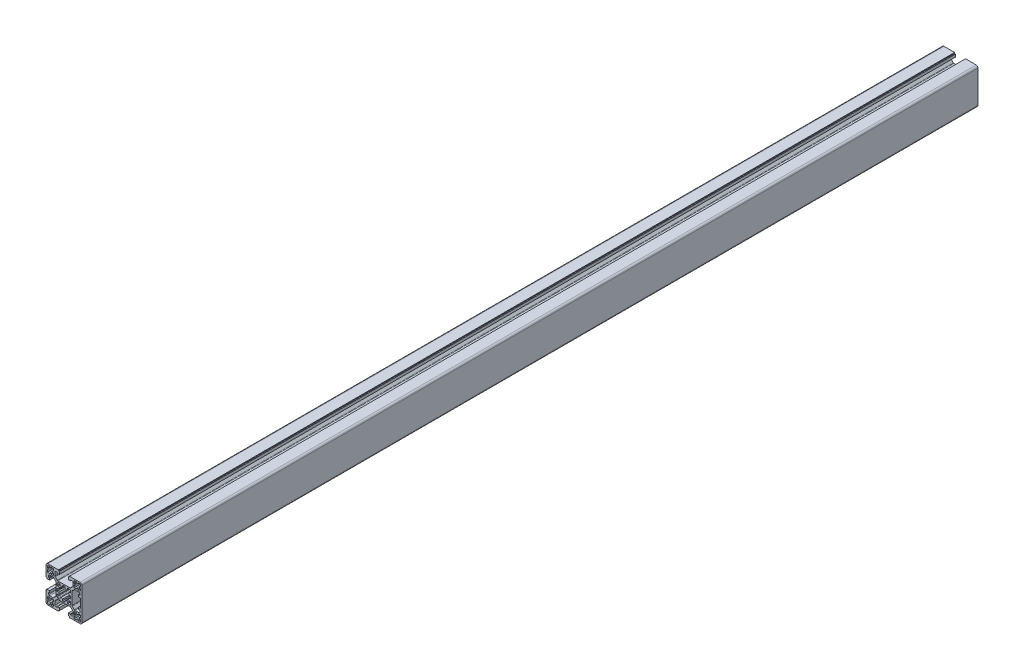
SolidWorks part; units mm, degrees
ref_plane "前视基准面" through (0, 0, 0) normal (0, 0, 1) x (1, 0, 0)
ref_plane "上视基准面" through (0, 0, 0) normal (0, 1, 0) x (1, 0, 0)
ref_plane "右视基准面" through (0, 0, 0) normal (1, 0, 0) x (0, 0, -1)
sketch "草图1" plane through (0, 0, 0) normal (0, 0, 1) x (1, 0, 0)
  line L0 (1011.2421, 717.8553) -> (1012.8421, 717.8553)
  line L1 (1015.5421, 689.5553) -> (1014.5421, 689.5553)
  line L2 (1015.5421, 686.8553) -> (1015.5421, 689.5553)
  line L3 (1012.8421, 686.8553) -> (1015.5421, 686.8553)
  line L4 (1012.8421, 687.8553) -> (1012.8421, 686.8553)
  line L5 (1011.2421, 687.8553) -> (1012.8421, 687.8553)
  line L6 (1011.2421, 686.8553) -> (1011.2421, 687.8553)
  line L7 (1009.5421, 686.8553) -> (1011.2421, 686.8553)
  line L8 (1008.5421, 689.5553) -> (1008.5421, 687.8553)
  line L9 (1009.5421, 689.5553) -> (1008.5421, 689.5553)
  line L10 (1009.5421, 691.1553) -> (1009.5421, 689.5553)
  line L11 (1008.5421, 691.1553) -> (1009.5421, 691.1553)
  line L12 (1008.5421, 693.8553) -> (1008.5421, 691.1553)
  line L13 (1011.2421, 693.8553) -> (1008.5421, 693.8553)
  line L14 (1011.2421, 692.8553) -> (1011.2421, 693.8553)
  line L15 (1012.8421, 692.8553) -> (1011.2421, 692.8553)
  line L16 (1012.8421, 693.8553) -> (1012.8421, 692.8553)
  line L17 (1015.5421, 693.8553) -> (1012.8421, 693.8553)
  line L18 (1015.5421, 691.1553) -> (1015.5421, 693.8553)
  line L19 (1014.5421, 691.1553) -> (1015.5421, 691.1553)
  line L20 (1014.5421, 689.5553) -> (1014.5421, 691.1553)
  line L21 (1042.8421, 693.8553) -> (1042.8421, 692.8553)
  line L22 (1045.5421, 693.8553) -> (1042.8421, 693.8553)
  line L23 (1045.5421, 691.1553) -> (1045.5421, 693.8553)
  line L24 (1044.5421, 691.1553) -> (1045.5421, 691.1553)
  line L25 (1044.5421, 689.5553) -> (1044.5421, 691.1553)
  line L26 (1045.5421, 689.5553) -> (1044.5421, 689.5553)
  line L27 (1045.5421, 687.8553) -> (1045.5421, 689.5553)
  line L28 (1042.8421, 686.8553) -> (1044.5421, 686.8553)
  line L29 (1042.8421, 687.8553) -> (1042.8421, 686.8553)
  line L30 (1041.2421, 687.8553) -> (1042.8421, 687.8553)
  line L31 (1041.2421, 686.8553) -> (1041.2421, 687.8553)
  line L32 (1038.5421, 686.8553) -> (1041.2421, 686.8553)
  line L33 (1038.5421, 689.5553) -> (1038.5421, 686.8553)
  line L34 (1039.5421, 689.5553) -> (1038.5421, 689.5553)
  line L35 (1039.5421, 691.1553) -> (1039.5421, 689.5553)
  line L36 (1038.5421, 691.1553) -> (1039.5421, 691.1553)
  line L37 (1038.5421, 693.8553) -> (1038.5421, 691.1553)
  line L38 (1041.2421, 693.8553) -> (1038.5421, 693.8553)
  line L39 (1041.2421, 692.8553) -> (1041.2421, 693.8553)
  line L40 (1042.8421, 692.8553) -> (1041.2421, 692.8553)
  line L41 (1025.6421, 697.8553) -> (1028.4421, 697.8553)
  line L42 (1025.6421, 699.5209) -> (1025.6421, 697.8553)
  line L43 (1022.8421, 699.1754) -> (1023.9066, 700.2398)
  line L44 (1022.8421, 697.8553) -> (1022.8421, 699.1754)
  line L45 (1020.5421, 697.8553) -> (1022.8421, 697.8553)
  line L46 (1019.5421, 701.1553) -> (1019.5421, 698.8553)
  line L47 (1020.8622, 701.1553) -> (1019.5421, 701.1553)
  line L48 (1021.9267, 702.2197) -> (1020.8622, 701.1553)
  line L49 (1019.5421, 703.9553) -> (1021.2078, 703.9553)
  line L50 (1019.5421, 706.7553) -> (1019.5421, 703.9553)
  line L51 (1021.2078, 706.7553) -> (1019.5421, 706.7553)
  line L52 (1020.8622, 709.5553) -> (1021.9267, 708.4909)
  line L53 (1019.5421, 709.5553) -> (1020.8622, 709.5553)
  line L54 (1019.5421, 711.8553) -> (1019.5421, 709.5553)
  line L55 (1022.8421, 712.8553) -> (1020.5421, 712.8553)
  line L56 (1022.8421, 711.5352) -> (1022.8421, 712.8553)
  line L57 (1023.9066, 710.4708) -> (1022.8421, 711.5352)
  line L58 (1025.6421, 712.8553) -> (1025.6421, 711.1897)
  line L59 (1028.4421, 712.8553) -> (1025.6421, 712.8553)
  line L60 (1028.4421, 711.1897) -> (1028.4421, 712.8553)
  line L61 (1031.2421, 711.5352) -> (1030.1777, 710.4708)
  line L62 (1031.2421, 712.8553) -> (1031.2421, 711.5352)
  line L63 (1033.5421, 712.8553) -> (1031.2421, 712.8553)
  line L64 (1034.5421, 709.5553) -> (1034.5421, 711.8553)
  line L65 (1033.222, 709.5553) -> (1034.5421, 709.5553)
  line L66 (1032.1576, 708.4909) -> (1033.222, 709.5553)
  line L67 (1034.5421, 706.7553) -> (1032.8765, 706.7553)
  line L68 (1034.5421, 703.9553) -> (1034.5421, 706.7553)
  line L69 (1032.8765, 703.9553) -> (1034.5421, 703.9553)
  line L70 (1033.222, 701.1553) -> (1032.1576, 702.2197)
  line L71 (1034.5421, 701.1553) -> (1033.222, 701.1553)
  line L72 (1034.5421, 698.8553) -> (1034.5421, 701.1553)
  line L73 (1031.2421, 697.8553) -> (1033.5421, 697.8553)
  line L74 (1031.2421, 699.1754) -> (1031.2421, 697.8553)
  line L75 (1030.1777, 700.2398) -> (1031.2421, 699.1754)
  line L76 (1028.4421, 697.8553) -> (1028.4421, 699.5209)
  line L77 (1043.0421, 700.2553) -> (1045.5421, 700.2553)
  line L78 (1043.0421, 698.2553) -> (1043.0421, 700.2553)
  line L79 (1045.0421, 698.2553) -> (1043.0421, 698.2553)
  line L80 (1045.0421, 696.3553) -> (1045.0421, 698.2553)
  line L81 (1039.2241, 695.3553) -> (1044.0421, 695.3553)
  line L82 (1036.335, 697.8302) -> (1038.517, 695.6482)
  line L83 (1036.0421, 712.1733) -> (1036.0421, 698.5373)
  line L84 (1038.517, 715.0624) -> (1036.335, 712.8804)
  line L85 (1044.0421, 715.3553) -> (1039.2241, 715.3553)
  line L86 (1045.0421, 712.4553) -> (1045.0421, 714.3553)
  line L87 (1043.0421, 712.4553) -> (1045.0421, 712.4553)
  line L88 (1043.0421, 710.4553) -> (1043.0421, 712.4553)
  line L89 (1045.5421, 710.4553) -> (1043.0421, 710.4553)
  line L90 (1045.5421, 700.2553) -> (1045.5421, 710.4553)
  line L91 (1019.9421, 688.3553) -> (1019.9421, 689.3553)
  line L92 (1018.0421, 688.3553) -> (1019.9421, 688.3553)
  line L93 (1017.0421, 693.1733) -> (1017.0421, 689.3553)
  line L94 (1019.517, 696.0624) -> (1017.335, 693.8804)
  line L95 (1033.8602, 696.3553) -> (1020.2241, 696.3553)
  line L96 (1036.7492, 693.8804) -> (1034.5673, 696.0624)
  line L97 (1037.0421, 689.3553) -> (1037.0421, 693.1733)
  line L98 (1034.1421, 688.3553) -> (1036.0421, 688.3553)
  line L99 (1034.1421, 689.3553) -> (1034.1421, 688.3553)
  line L100 (1032.1421, 689.3553) -> (1034.1421, 689.3553)
  line L101 (1032.1421, 686.3553) -> (1032.1421, 689.3553)
  line L102 (1033.1421, 686.3553) -> (1032.1421, 686.3553)
  line L103 (1033.1421, 685.3553) -> (1033.1421, 686.3553)
  line L104 (1045.0421, 685.3553) -> (1033.1421, 685.3553)
  line L105 (1047.0421, 723.3553) -> (1047.0421, 687.3553)
  line L106 (1033.1421, 725.3553) -> (1045.0421, 725.3553)
  line L107 (1033.1421, 724.3553) -> (1033.1421, 725.3553)
  line L108 (1032.1421, 724.3553) -> (1033.1421, 724.3553)
  line L109 (1032.1421, 721.3553) -> (1032.1421, 724.3553)
  line L110 (1034.1421, 721.3553) -> (1032.1421, 721.3553)
  line L111 (1034.1421, 722.3553) -> (1034.1421, 721.3553)
  line L112 (1036.0421, 722.3553) -> (1034.1421, 722.3553)
  line L113 (1037.0421, 717.5373) -> (1037.0421, 721.3553)
  line L114 (1034.5673, 714.6482) -> (1036.7492, 716.8302)
  line L115 (1020.2241, 714.3553) -> (1033.8602, 714.3553)
  line L116 (1017.335, 716.8302) -> (1019.517, 714.6482)
  line L117 (1017.0421, 721.3553) -> (1017.0421, 717.5373)
  line L118 (1019.9421, 722.3553) -> (1018.0421, 722.3553)
  line L119 (1019.9421, 721.3553) -> (1019.9421, 722.3553)
  line L120 (1021.9421, 721.3553) -> (1019.9421, 721.3553)
  line L121 (1021.9421, 724.3553) -> (1021.9421, 721.3553)
  line L122 (1020.9421, 724.3553) -> (1021.9421, 724.3553)
  line L123 (1020.9421, 725.3553) -> (1020.9421, 724.3553)
  line L124 (1009.0421, 725.3553) -> (1020.9421, 725.3553)
  line L125 (1007.0421, 711.4553) -> (1007.0421, 723.3553)
  line L126 (1008.0421, 711.4553) -> (1007.0421, 711.4553)
  line L127 (1008.0421, 710.4553) -> (1008.0421, 711.4553)
  line L128 (1011.0421, 710.4553) -> (1008.0421, 710.4553)
  line L129 (1011.0421, 712.4553) -> (1011.0421, 710.4553)
  line L130 (1010.0421, 712.4553) -> (1011.0421, 712.4553)
  line L131 (1010.0421, 714.3553) -> (1010.0421, 712.4553)
  line L132 (1014.8602, 715.3553) -> (1011.0421, 715.3553)
  line L133 (1017.7492, 712.8804) -> (1015.5673, 715.0624)
  line L134 (1018.0421, 698.5373) -> (1018.0421, 712.1733)
  line L135 (1015.5673, 695.6482) -> (1017.7492, 697.8302)
  line L136 (1011.0421, 695.3553) -> (1014.8602, 695.3553)
  line L137 (1010.0421, 698.2553) -> (1010.0421, 696.3553)
  line L138 (1011.0421, 698.2553) -> (1010.0421, 698.2553)
  line L139 (1011.0421, 700.2553) -> (1011.0421, 698.2553)
  line L140 (1008.0421, 700.2553) -> (1011.0421, 700.2553)
  line L141 (1008.0421, 699.2553) -> (1008.0421, 700.2553)
  line L142 (1007.0421, 699.2553) -> (1008.0421, 699.2553)
  line L143 (1007.0421, 687.3553) -> (1007.0421, 699.2553)
  line L144 (1020.9421, 685.3553) -> (1009.0421, 685.3553)
  line L145 (1020.9421, 686.3553) -> (1020.9421, 685.3553)
  line L146 (1021.9421, 686.3553) -> (1020.9421, 686.3553)
  line L147 (1021.9421, 689.3553) -> (1021.9421, 686.3553)
  line L148 (1019.9421, 689.3553) -> (1021.9421, 689.3553)
  line L149 (1038.5421, 721.1553) -> (1039.5421, 721.1553)
  line L150 (1038.5421, 723.8553) -> (1038.5421, 721.1553)
  line L151 (1041.2421, 723.8553) -> (1038.5421, 723.8553)
  line L152 (1041.2421, 722.8553) -> (1041.2421, 723.8553)
  line L153 (1042.8421, 722.8553) -> (1041.2421, 722.8553)
  line L154 (1042.8421, 723.8553) -> (1042.8421, 722.8553)
  line L155 (1044.5421, 723.8553) -> (1042.8421, 723.8553)
  line L156 (1045.5421, 721.1553) -> (1045.5421, 722.8553)
  line L157 (1044.5421, 721.1553) -> (1045.5421, 721.1553)
  line L158 (1044.5421, 719.5553) -> (1044.5421, 721.1553)
  line L159 (1045.5421, 719.5553) -> (1044.5421, 719.5553)
  line L160 (1045.5421, 716.8553) -> (1045.5421, 719.5553)
  line L161 (1042.8421, 716.8553) -> (1045.5421, 716.8553)
  line L162 (1042.8421, 717.8553) -> (1042.8421, 716.8553)
  line L163 (1041.2421, 717.8553) -> (1042.8421, 717.8553)
  line L164 (1041.2421, 716.8553) -> (1041.2421, 717.8553)
  line L165 (1038.5421, 716.8553) -> (1041.2421, 716.8553)
  line L166 (1038.5421, 719.5553) -> (1038.5421, 716.8553)
  line L167 (1039.5421, 719.5553) -> (1038.5421, 719.5553)
  line L168 (1039.5421, 721.1553) -> (1039.5421, 719.5553)
  line L169 (1011.2421, 716.8553) -> (1011.2421, 717.8553)
  line L170 (1008.5421, 716.8553) -> (1011.2421, 716.8553)
  line L171 (1008.5421, 719.5553) -> (1008.5421, 716.8553)
  line L172 (1009.5421, 719.5553) -> (1008.5421, 719.5553)
  line L173 (1009.5421, 721.1553) -> (1009.5421, 719.5553)
  line L174 (1008.5421, 721.1553) -> (1009.5421, 721.1553)
  line L175 (1008.5421, 722.8553) -> (1008.5421, 721.1553)
  line L176 (1011.2421, 723.8553) -> (1009.5421, 723.8553)
  line L177 (1011.2421, 722.8553) -> (1011.2421, 723.8553)
  line L178 (1012.8421, 722.8553) -> (1011.2421, 722.8553)
  line L179 (1012.8421, 723.8553) -> (1012.8421, 722.8553)
  line L180 (1015.5421, 723.8553) -> (1012.8421, 723.8553)
  line L181 (1015.5421, 721.1553) -> (1015.5421, 723.8553)
  line L182 (1014.5421, 721.1553) -> (1015.5421, 721.1553)
  line L183 (1014.5421, 719.5553) -> (1014.5421, 721.1553)
  line L184 (1015.5421, 719.5553) -> (1014.5421, 719.5553)
  line L185 (1015.5421, 716.8553) -> (1015.5421, 719.5553)
  line L186 (1012.8421, 716.8553) -> (1015.5421, 716.8553)
  line L187 (1012.8421, 717.8553) -> (1012.8421, 716.8553)
  arc A0 (1045.5421, 722.8553) -> (1044.5421, 723.8553) centre (1044.5421, 722.8553) ccw
  arc A1 (1009.5421, 723.8553) -> (1008.5421, 722.8553) centre (1009.5421, 722.8553) ccw
  arc A2 (1008.5421, 687.8553) -> (1009.5421, 686.8553) centre (1009.5421, 687.8553) ccw
  arc A3 (1044.5421, 686.8553) -> (1045.5421, 687.8553) centre (1044.5421, 687.8553) ccw
  arc A4 (1023.9066, 700.2398) -> (1025.6421, 699.5209) centre (1027.0421, 705.3553) ccw
  arc A5 (1019.5421, 698.8553) -> (1020.5421, 697.8553) centre (1020.5421, 698.8553) ccw
  arc A6 (1021.2078, 703.9553) -> (1021.9267, 702.2197) centre (1027.0421, 705.3553) ccw
  arc A7 (1021.9267, 708.4909) -> (1021.2078, 706.7553) centre (1027.0421, 705.3553) ccw
  arc A8 (1020.5421, 712.8553) -> (1019.5421, 711.8553) centre (1020.5421, 711.8553) ccw
  arc A9 (1025.6421, 711.1897) -> (1023.9066, 710.4708) centre (1027.0421, 705.3553) ccw
  arc A10 (1030.1777, 710.4708) -> (1028.4421, 711.1897) centre (1027.0421, 705.3553) ccw
  arc A11 (1034.5421, 711.8553) -> (1033.5421, 712.8553) centre (1033.5421, 711.8553) ccw
  arc A12 (1032.8765, 706.7553) -> (1032.1576, 708.4909) centre (1027.0421, 705.3553) ccw
  arc A13 (1032.1576, 702.2197) -> (1032.8765, 703.9553) centre (1027.0421, 705.3553) ccw
  arc A14 (1033.5421, 697.8553) -> (1034.5421, 698.8553) centre (1033.5421, 698.8553) ccw
  arc A15 (1028.4421, 699.5209) -> (1030.1777, 700.2398) centre (1027.0421, 705.3553) ccw
  arc A16 (1044.0421, 695.3553) -> (1045.0421, 696.3553) centre (1044.0421, 696.3553) ccw
  arc A17 (1038.517, 695.6482) -> (1039.2241, 695.3553) centre (1039.2241, 696.3553) ccw
  arc A18 (1036.0421, 698.5373) -> (1036.335, 697.8302) centre (1037.0421, 698.5373) ccw
  arc A19 (1036.335, 712.8804) -> (1036.0421, 712.1733) centre (1037.0421, 712.1733) ccw
  arc A20 (1039.2241, 715.3553) -> (1038.517, 715.0624) centre (1039.2241, 714.3553) ccw
  arc A21 (1045.0421, 714.3553) -> (1044.0421, 715.3553) centre (1044.0421, 714.3553) ccw
  arc A22 (1017.0421, 689.3553) -> (1018.0421, 688.3553) centre (1018.0421, 689.3553) ccw
  arc A23 (1017.335, 693.8804) -> (1017.0421, 693.1733) centre (1018.0421, 693.1733) ccw
  arc A24 (1020.2241, 696.3553) -> (1019.517, 696.0624) centre (1020.2241, 695.3553) ccw
  arc A25 (1034.5673, 696.0624) -> (1033.8602, 696.3553) centre (1033.8602, 695.3553) ccw
  arc A26 (1037.0421, 693.1733) -> (1036.7492, 693.8804) centre (1036.0421, 693.1733) ccw
  arc A27 (1036.0421, 688.3553) -> (1037.0421, 689.3553) centre (1036.0421, 689.3553) ccw
  arc A28 (1045.0421, 685.3553) -> (1047.0421, 687.3553) centre (1045.0421, 687.3553) ccw
  arc A29 (1047.0421, 723.3553) -> (1045.0421, 725.3553) centre (1045.0421, 723.3553) ccw
  arc A30 (1037.0421, 721.3553) -> (1036.0421, 722.3553) centre (1036.0421, 721.3553) ccw
  arc A31 (1036.7492, 716.8302) -> (1037.0421, 717.5373) centre (1036.0421, 717.5373) ccw
  arc A32 (1033.8602, 714.3553) -> (1034.5673, 714.6482) centre (1033.8602, 715.3553) ccw
  arc A33 (1019.517, 714.6482) -> (1020.2241, 714.3553) centre (1020.2241, 715.3553) ccw
  arc A34 (1017.0421, 717.5373) -> (1017.335, 716.8302) centre (1018.0421, 717.5373) ccw
  arc A35 (1018.0421, 722.3553) -> (1017.0421, 721.3553) centre (1018.0421, 721.3553) ccw
  arc A36 (1009.0421, 725.3553) -> (1007.0421, 723.3553) centre (1009.0421, 723.3553) ccw
  arc A37 (1011.0421, 715.3553) -> (1010.0421, 714.3553) centre (1011.0421, 714.3553) ccw
  arc A38 (1015.5673, 715.0624) -> (1014.8602, 715.3553) centre (1014.8602, 714.3553) ccw
  arc A39 (1018.0421, 712.1733) -> (1017.7492, 712.8804) centre (1017.0421, 712.1733) ccw
  arc A40 (1017.7492, 697.8302) -> (1018.0421, 698.5373) centre (1017.0421, 698.5373) ccw
  arc A41 (1014.8602, 695.3553) -> (1015.5673, 695.6482) centre (1014.8602, 696.3553) ccw
  arc A42 (1010.0421, 696.3553) -> (1011.0421, 695.3553) centre (1011.0421, 696.3553) ccw
  arc A43 (1007.0421, 687.3553) -> (1009.0421, 685.3553) centre (1009.0421, 687.3553) ccw
extrude "拉伸1" add sketch "草图1" along normal blind 1000
